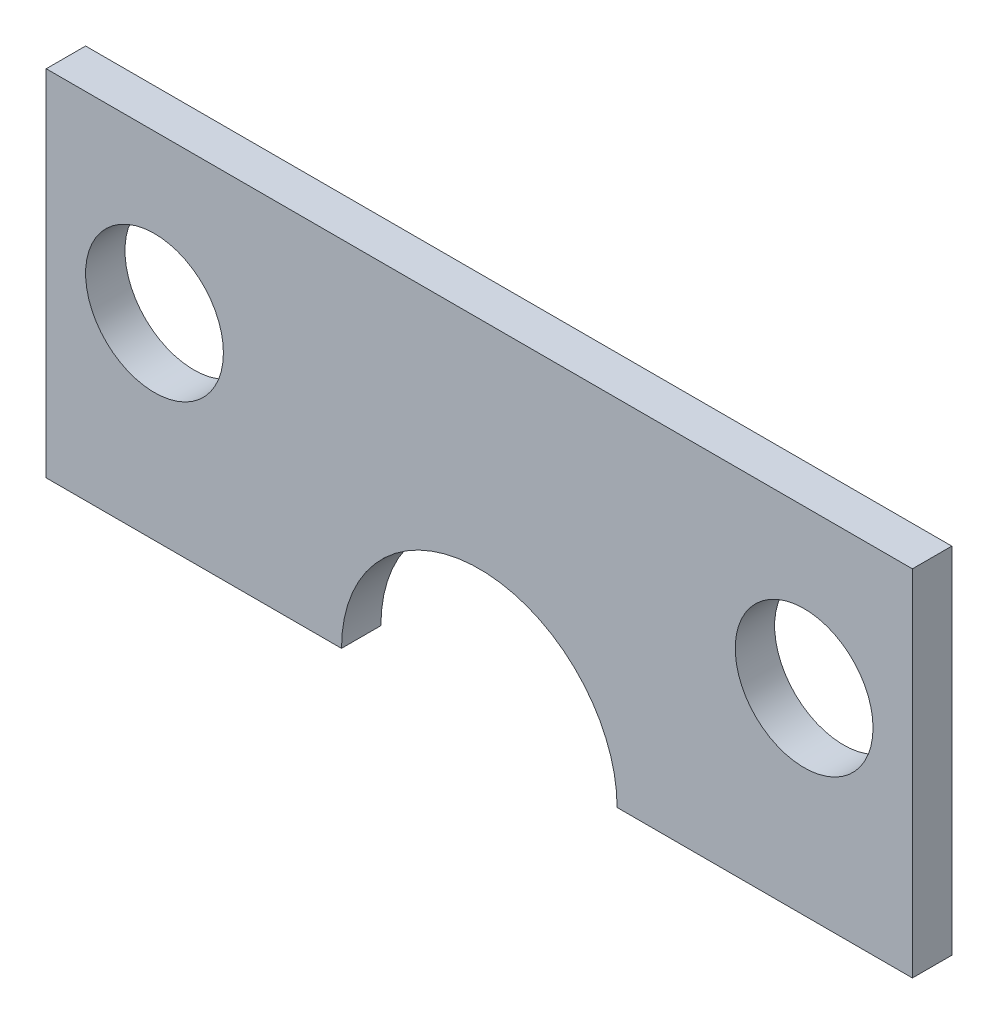
SolidWorks part; units mm, degrees
ref_plane "Front Plane" through (0, 0, 0) normal (0, 0, 1) x (1, 0, 0)
ref_plane "Top Plane" through (0, 0, 0) normal (0, 1, 0) x (1, 0, 0)
ref_plane "Right Plane" through (0, 0, 0) normal (1, 0, 0) x (0, 0, -1)
sketch "Sketch1" plane through (0, 0, 0) normal (0, 0, 1) x (1, 0, 0)
  line L1 (-74.2897, -54.3468) -> (-30.2897, -54.3468)
  line L2 (-74.2897, -54.3468) -> (-74.2897, -72.3468)
  line L3 (-74.2897, -72.3468) -> (-30.2897, -72.3468)
  line L4 (-30.2897, -54.3468) -> (-30.2897, -72.3468)
  dimension "D1" = 44
extrude "Boss-Extrude1" add sketch "Sketch1" against normal blind 2
sketch "Sketch7" plane through (0, 0, 0) normal (0, 0, 1) x (1, 0, 0)
  line L0 (-74.2897, -72.3468) -> (-30.2897, -72.3468) construction
  arc A0 (-45.2897, -72.3468) -> (-59.2897, -72.3468) centre (-52.2897, -72.3468) ccw
  dimension "D1" = 22
extrude "Cut-Extrude3" cut sketch "Sketch7" against normal blind 2 and the other way through all
sketch "Sketch8" plane through (0, 0, 0) normal (0, 0, 1) x (1, 0, 0)
  line L0 (-74.2897, -72.3468) -> (-59.2897, -72.3468) construction
  line L1 (-74.2897, -54.3468) -> (-74.2897, -72.3468) construction
  circle A0 centre (-68.7897, -62.3468) radius 3.5
  dimension "D1" = 10
  dimension "D2" = 5.5
extrude "Cut-Extrude4" cut sketch "Sketch8" against normal blind 2.8
sketch "Sketch9" plane through (0, 0, 0) normal (0, 0, 1) x (1, 0, 0)
  line L0 (-30.2897, -72.3468) -> (-30.2897, -54.3468) construction
  line L1 (-45.2897, -72.3468) -> (-30.2897, -72.3468) construction
  circle A0 centre (-35.7897, -62.3468) radius 3.5
  dimension "D1" = 5.5
  dimension "D2" = 10
extrude "Cut-Extrude5" cut sketch "Sketch9" against normal blind 2.8
